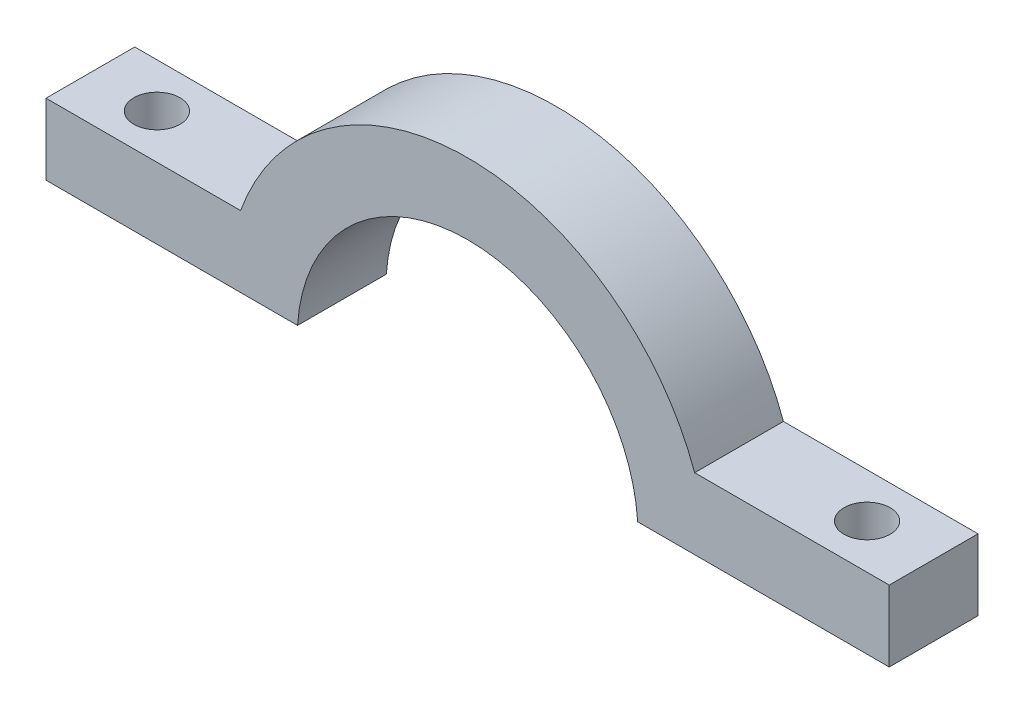
SolidWorks part; units mm, degrees
ref_plane "Front Plane" through (0, 0, 0) normal (0, 0, 1) x (1, 0, 0)
ref_plane "Top Plane" through (0, 0, 0) normal (0, 1, 0) x (1, 0, 0)
ref_plane "Right Plane" through (0, 0, 0) normal (1, 0, 0) x (0, 0, -1)
sketch "Sketch1" plane through (0, 0, 0) normal (0, 0, 1) x (1, 0, 0)
  line L0 (-16.2426, 5.8737) -> (-30.1625, 5.8737) construction
  line L1 (-30.1625, 5.8737) -> (-30.1625, 0.7937) construction
  line L2 (-30.1625, 0.7937) -> (-12.1661, 0.7937) construction
  line L3 (30.1625, 0.7938) -> (12.1661, 0.7938) construction
  line L4 (30.1625, 5.8738) -> (30.1625, 0.7938) construction
  line L5 (16.2426, 5.8738) -> (30.1625, 5.8738) construction
  line L6 (-16.2426, 5.8737) -> (-30.1625, 5.8737)
  line L7 (-30.1625, 5.8737) -> (-30.1625, 0.7937)
  line L8 (-30.1625, 0.7937) -> (-12.1661, 0.7937)
  line L9 (30.1625, 0.7938) -> (12.1661, 0.7938)
  line L10 (30.1625, 5.8738) -> (30.1625, 0.7938)
  line L11 (16.2426, 5.8738) -> (30.1625, 5.8738)
  arc A0 (12.1661, 0.7938) -> (-12.1661, 0.7937) centre (0, 0) ccw construction
  arc A1 (16.2426, 5.8738) -> (-16.2426, 5.8737) centre (0, 0) ccw construction
  arc A2 (12.1661, 0.7938) -> (-12.1661, 0.7937) centre (0, 0) ccw
  arc A3 (16.2426, 5.8738) -> (-16.2426, 5.8737) centre (0, 0) ccw
extrude "Boss-Extrude1" add sketch "Sketch1" along normal blind 6.35
sketch "Sketch2" plane through (0, 5.8737, 0) normal (0, 1, 0) x (1, 0, 0)
  line L0 (-30.1625, -3.175) -> (30.1625, -3.175) construction
  line L1 (-30.1625, -6.35) -> (-30.1625, 0) construction
  line L2 (30.1625, -6.35) -> (30.1625, 0) construction
  circle A0 centre (-25.4, -3.175) radius 1.651
  circle A1 centre (25.4, -3.175) radius 1.651
  dimension "D1" = 3.302
  dimension "D2" = 50.8
  dimension "D3" = 25.4
extrude "Cut-Extrude1" cut sketch "Sketch2" against normal blind 6.35
